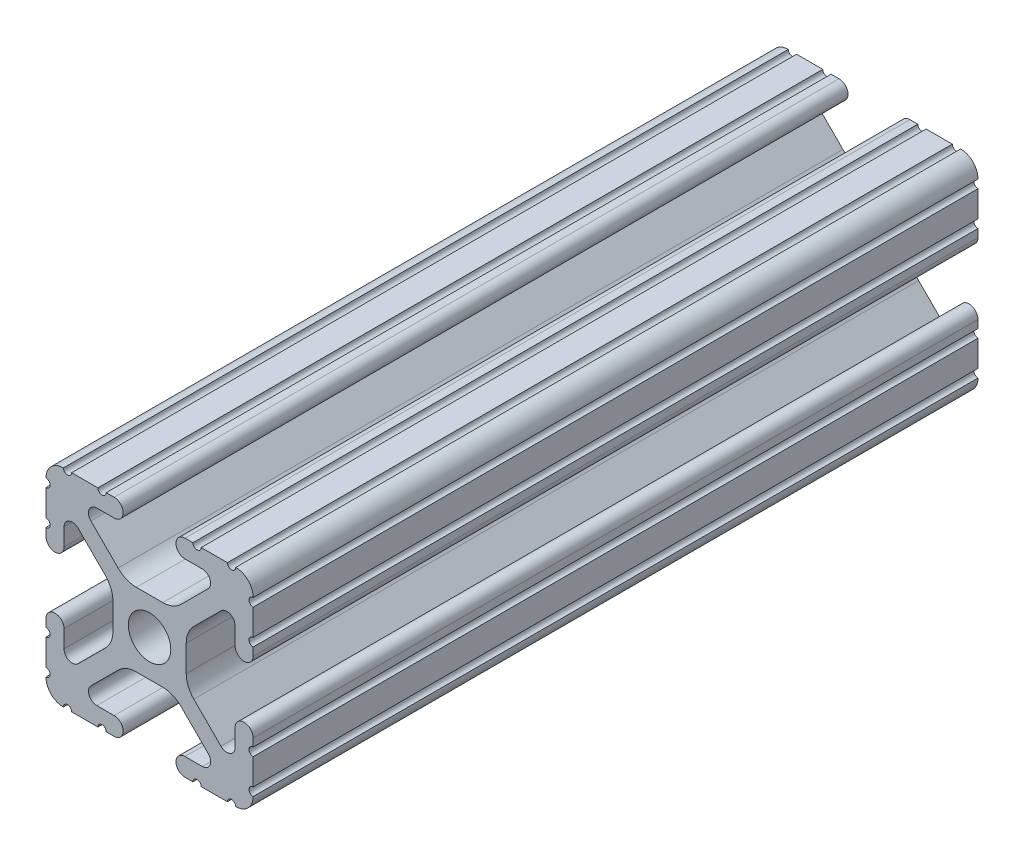
SolidWorks part; units mm, degrees
material "6061-T6 (SS)"
ref_plane "Front Plane" through (0, 0, 0) normal (0, 0, 1) x (1, 0, 0)
ref_plane "Top Plane" through (0, 0, 0) normal (0, 1, 0) x (1, 0, 0)
ref_plane "Right Plane" through (0, 0, 0) normal (1, 0, 0) x (0, 0, -1)
ref_plane "Plane1" through (0, 0, -450.85) normal (0, 0, -1) x (-1, 0, 0)
sketch "Sketch1" plane through (0, 0, -450.85) normal (0, 0, -1) x (-1, 0, 0)
  line L0 (12.7, -9.5504) -> (12.7, -6.3331)
  line L1 (12.7, -5.3171) -> (12.7, -4.3434)
  line L2 (10.4902, -4.3434) -> (10.4902, -6.4748)
  line L3 (8.7558, -7.1932) -> (5.4257, -3.8632)
  line L4 (4.4958, -1.6181) -> (4.4958, 1.6181)
  line L5 (5.4257, 3.8632) -> (8.7558, 7.1932)
  line L6 (10.4902, 6.4748) -> (10.4902, 4.3434)
  line L7 (12.7, 4.3434) -> (12.7, 5.3171)
  line L8 (12.7, 6.3331) -> (12.7, 9.5504)
  line L9 (9.5504, 12.7) -> (6.3331, 12.7)
  line L10 (5.3171, 12.7) -> (4.3434, 12.7)
  line L11 (4.3434, 10.4902) -> (6.4748, 10.4902)
  line L12 (7.1932, 8.7558) -> (3.8632, 5.4257)
  line L13 (1.6181, 4.4958) -> (-1.6181, 4.4958)
  line L14 (-3.8632, 5.4257) -> (-7.1932, 8.7558)
  line L15 (-6.4748, 10.4902) -> (-4.3434, 10.4902)
  line L16 (-4.3434, 12.7) -> (-5.3171, 12.7)
  line L17 (-6.3331, 12.7) -> (-9.5504, 12.7)
  line L18 (-12.7, 9.5504) -> (-12.7, 6.3331)
  line L19 (-12.7, 5.3171) -> (-12.7, 4.3434)
  line L20 (-10.4902, 4.3434) -> (-10.4902, 6.4748)
  line L21 (-8.7558, 7.1932) -> (-5.4257, 3.8632)
  line L22 (-4.4958, 1.6181) -> (-4.4958, -1.6181)
  line L23 (-5.4257, -3.8632) -> (-8.7558, -7.1932)
  line L24 (-10.4902, -6.4748) -> (-10.4902, -4.3434)
  line L25 (-12.7, -4.3434) -> (-12.7, -5.3171)
  line L26 (-12.7, -6.3331) -> (-12.7, -9.5504)
  line L27 (-9.5504, -12.7) -> (-6.3331, -12.7)
  line L28 (-5.3171, -12.7) -> (-4.3434, -12.7)
  line L29 (-4.3434, -10.4902) -> (-6.4748, -10.4902)
  line L30 (-7.1932, -8.7558) -> (-3.8632, -5.4257)
  line L31 (-1.6181, -4.4958) -> (1.6181, -4.4958)
  line L32 (3.8632, -5.4257) -> (7.1932, -8.7558)
  line L33 (6.4748, -10.4902) -> (4.3434, -10.4902)
  line L34 (4.3434, -12.7) -> (5.3171, -12.7)
  line L35 (6.3331, -12.7) -> (9.5504, -12.7)
  arc A0 (12.6998, -10.5664) -> (12.7, -9.5504) centre (12.7, -10.0584) cw
  arc A1 (12.7, -6.3331) -> (12.7, -5.3171) centre (12.7, -5.8251) cw
  arc A2 (12.7, -4.3434) -> (10.4902, -4.3434) centre (11.5951, -4.3434) ccw
  arc A3 (10.4902, -6.4748) -> (8.7558, -7.1932) centre (9.4742, -6.4748) cw
  arc A4 (5.4257, -3.8632) -> (4.4958, -1.6181) centre (7.6708, -1.6181) cw
  arc A5 (4.4958, 1.6181) -> (5.4257, 3.8632) centre (7.6708, 1.6181) cw
  arc A6 (8.7558, 7.1932) -> (10.4902, 6.4748) centre (9.4742, 6.4748) cw
  arc A7 (10.4902, 4.3434) -> (12.7, 4.3434) centre (11.5951, 4.3434) ccw
  arc A8 (12.7, 5.3171) -> (12.7, 6.3331) centre (12.7, 5.8251) cw
  arc A9 (12.7, 9.5504) -> (12.6998, 10.5664) centre (12.7, 10.0584) cw
  arc A10 (12.6998, 10.5664) -> (10.5664, 12.6998) centre (10.5918, 10.5918) ccw
  arc A11 (10.5664, 12.6998) -> (9.5504, 12.7) centre (10.0584, 12.7) cw
  arc A12 (6.3331, 12.7) -> (5.3171, 12.7) centre (5.8251, 12.7) cw
  arc A13 (4.3434, 12.7) -> (4.3434, 10.4902) centre (4.3434, 11.5951) ccw
  arc A14 (6.4748, 10.4902) -> (7.1932, 8.7558) centre (6.4748, 9.4742) cw
  arc A15 (3.8632, 5.4257) -> (1.6181, 4.4958) centre (1.6181, 7.6708) cw
  arc A16 (-1.6181, 4.4958) -> (-3.8632, 5.4257) centre (-1.6181, 7.6708) cw
  arc A17 (-7.1932, 8.7558) -> (-6.4748, 10.4902) centre (-6.4748, 9.4742) cw
  arc A18 (-4.3434, 10.4902) -> (-4.3434, 12.7) centre (-4.3434, 11.5951) ccw
  arc A19 (-5.3171, 12.7) -> (-6.3331, 12.7) centre (-5.8251, 12.7) cw
  arc A20 (-9.5504, 12.7) -> (-10.5664, 12.6998) centre (-10.0584, 12.7) cw
  arc A21 (-10.5664, 12.6998) -> (-12.6998, 10.5664) centre (-10.5918, 10.5918) ccw
  arc A22 (-12.6998, 10.5664) -> (-12.7, 9.5504) centre (-12.7, 10.0584) cw
  arc A23 (-12.7, 6.3331) -> (-12.7, 5.3171) centre (-12.7, 5.8251) cw
  arc A24 (-12.7, 4.3434) -> (-10.4902, 4.3434) centre (-11.5951, 4.3434) ccw
  arc A25 (-10.4902, 6.4748) -> (-8.7558, 7.1932) centre (-9.4742, 6.4748) cw
  arc A26 (-5.4257, 3.8632) -> (-4.4958, 1.6181) centre (-7.6708, 1.6181) cw
  arc A27 (-4.4958, -1.6181) -> (-5.4257, -3.8632) centre (-7.6708, -1.6181) cw
  arc A28 (-8.7558, -7.1932) -> (-10.4902, -6.4748) centre (-9.4742, -6.4748) cw
  arc A29 (-10.4902, -4.3434) -> (-12.7, -4.3434) centre (-11.5951, -4.3434) ccw
  arc A30 (-12.7, -5.3171) -> (-12.7, -6.3331) centre (-12.7, -5.8251) cw
  arc A31 (-12.7, -9.5504) -> (-12.6998, -10.5664) centre (-12.7, -10.0584) cw
  arc A32 (-12.6998, -10.5664) -> (-10.5664, -12.6998) centre (-10.5918, -10.5918) ccw
  arc A33 (-10.5664, -12.6998) -> (-9.5504, -12.7) centre (-10.0584, -12.7) cw
  arc A34 (-6.3331, -12.7) -> (-5.3171, -12.7) centre (-5.8251, -12.7) cw
  arc A35 (-4.3434, -12.7) -> (-4.3434, -10.4902) centre (-4.3434, -11.5951) ccw
  arc A36 (-6.4748, -10.4902) -> (-7.1932, -8.7558) centre (-6.4748, -9.4742) cw
  arc A37 (-3.8632, -5.4257) -> (-1.6181, -4.4958) centre (-1.6181, -7.6708) cw
  arc A38 (1.6181, -4.4958) -> (3.8632, -5.4257) centre (1.6181, -7.6708) cw
  arc A39 (7.1932, -8.7558) -> (6.4748, -10.4902) centre (6.4748, -9.4742) cw
  arc A40 (4.3434, -10.4902) -> (4.3434, -12.7) centre (4.3434, -11.5951) ccw
  arc A41 (5.3171, -12.7) -> (6.3331, -12.7) centre (5.8251, -12.7) cw
  arc A42 (9.5504, -12.7) -> (10.5664, -12.6998) centre (10.0584, -12.7) cw
  arc A43 (10.5664, -12.6998) -> (12.6998, -10.5664) centre (10.5918, -10.5918) ccw
  circle A44 centre (0, 0) radius 2.6035
extrude "Boss-Extrude1" add sketch "Sketch1" against normal mid plane 88.9
